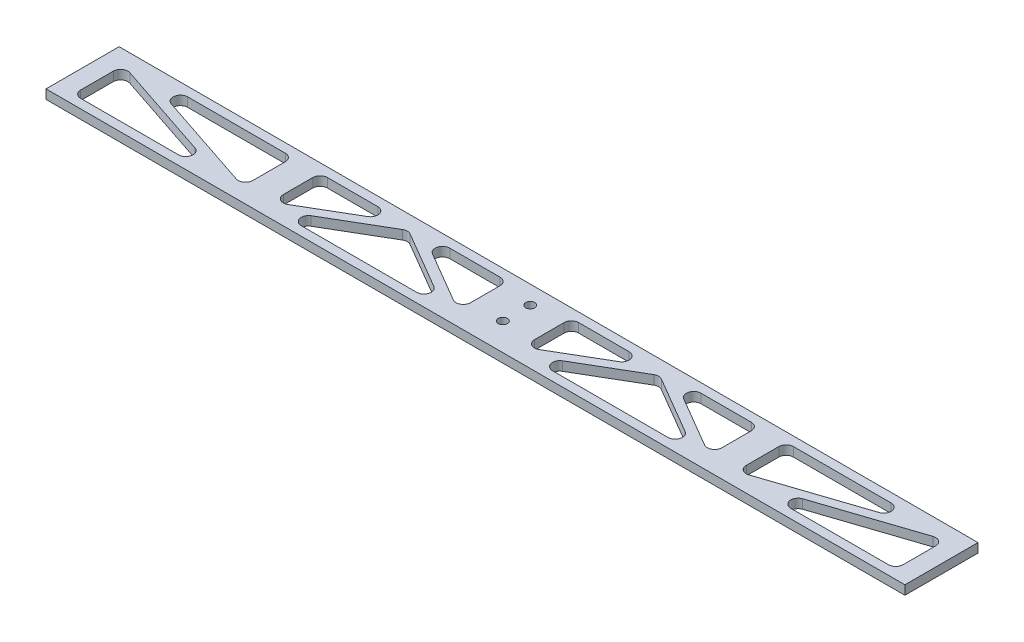
SolidWorks part; units mm, degrees
material "Balsa"
ref_plane "Front Plane" through (0, 0, 0) normal (0, 0, 1) x (1, 0, 0)
ref_plane "Top Plane" through (0, 0, 0) normal (0, 1, 0) x (1, 0, 0)
ref_plane "Right Plane" through (0, 0, 0) normal (1, 0, 0) x (0, 0, -1)
sketch "Sketch1" plane through (0, 0, 0) normal (0, 1, 0) x (1, 0, 0)
  line L1 (149.225, -12.7) -> (-149.225, -12.7)
  line L2 (149.225, -12.7) -> (149.225, 12.7)
  line L3 (149.225, 12.7) -> (-149.225, 12.7)
  line L4 (-149.225, -12.7) -> (-149.225, 12.7)
  point P0 (0, 12.7)
  point P6 (-149.225, 0)
  dimension "D1" = 25.4
  dimension "D2" = 298.45
extrude "Boss-Extrude1" add sketch "Sketch1" along normal blind 3.175
sketch "Sketch2" plane through (0, 3.175, 0) normal (0, 1, 0) x (1, 0, 0)
  line L0 (149.225, -12.7) -> (149.225, 12.7) construction
  line L2 (-149.225, 12.7) -> (-149.225, -12.7) construction
  line L4 (149.225, -12.7) -> (149.225, 12.7)
  line L6 (-149.225, 12.7) -> (-149.225, -12.7)
  line L8 (149.225, 9.525) -> (-149.225, 9.525)
  line L9 (-149.225, -9.525) -> (149.225, -9.525)
  line L10 (-142.875, 9.525) -> (-142.875, -9.525)
  line L11 (-80.9625, 9.525) -> (-80.9625, -9.525) construction
  line L12 (142.875, 9.525) -> (142.875, -9.525)
  line L13 (0, -9.525) -> (0, 9.525) construction
  line L14 (11.1125, 9.525) -> (11.1125, -9.525)
  line L15 (-11.1125, 9.525) -> (-11.1125, -9.525)
  line L16 (-85.725, 9.525) -> (-85.725, -9.525)
  line L17 (-76.2, 9.525) -> (-76.2, -9.525)
  line L18 (80.9625, 9.525) -> (80.9625, -9.525) construction
  line L19 (85.725, 9.525) -> (85.725, -9.525)
  line L20 (76.2, 9.525) -> (76.2, -9.525)
  line L21 (-76.2, -9.525) -> (-43.6562, 9.525)
  line L22 (-43.6562, 9.525) -> (-11.1125, -9.525)
  line L23 (-85.725, -9.525) -> (-142.875, 9.525)
  line L24 (11.1125, -9.525) -> (43.6562, 9.525)
  line L25 (43.6562, 9.525) -> (76.2, -9.525)
  line L26 (85.725, -9.525) -> (142.875, 9.525)
  line L27 (-85.223, -8.019) -> (-142.373, 11.031)
  line L28 (-75.398, -10.895) -> (-43.6562, 7.6855)
  line L29 (-43.6562, 7.6855) -> (-11.9145, -10.895)
  line L30 (11.9145, -10.895) -> (43.6562, 7.6855)
  line L31 (43.6562, 7.6855) -> (75.398, -10.895)
  line L32 (86.227, -11.031) -> (143.377, 8.019)
  line L33 (-86.227, -11.031) -> (-143.377, 8.019)
  line L34 (-77.002, -8.155) -> (-43.6562, 11.3645)
  line L35 (-43.6562, 11.3645) -> (-10.3105, -8.155)
  line L36 (10.3105, -8.155) -> (43.6562, 11.3645)
  line L37 (43.6562, 11.3645) -> (77.002, -8.155)
  line L38 (85.223, -8.019) -> (142.373, 11.031)
  dimension "D1" = 3.175
  dimension "D2" = 3.175
  dimension "D3" = 6.35
  dimension "D4" = 6.35
  dimension "D11" = 4.7625
  dimension "D12" = 4.7625
  dimension "D8" = 9.525
  dimension "D9" = 4.7625
  dimension "D7" = 63.5
  dimension "D10" = 63.5
  dimension "D5" = 22.225
  dimension "D6" = 11.1125
  dimension "D13" = 1.5875
  dimension "D14" = 1.5875
extrude "Cut-Extrude1" cut sketch "Sketch2" against normal through all contours L9 L33 L10 | L27 L16 L8 | L17 L34 L8 | L29 L28 L9 | L8 L35 L15 | L14 L36 L8 | L31 L30 L9 | L8 L37 L20 | L19 L38 L8 | L32 L9 L12
sketch "Sketch3" plane through (0, 3.175, 0) normal (0, 1, 0) x (1, 0, 0)
  circle A0 centre (0, 6.35) radius 1.5875
  circle A1 centre (0, -3.175) radius 1.5875
  dimension "D1" = 3.175
  dimension "D2" = 9.525
  dimension "D3" = 6.35
extrude "Cut-Extrude2" cut sketch "Sketch3" against normal through all
fillet "Fillet1" radius 2.54 30 edges at (-14.2549, 1.5875, 9.525) (-73.0576, 1.5875, 9.525) (-43.6562, 1.5875, -7.6855) (-11.1125, 1.5875, 7.6855) (-40.5138, 1.5875, -9.525) (-11.1125, 1.5875, -9.525) (-46.7987, 1.5875, -9.525) (-76.2, 1.5875, 7.6855) (-76.2, 1.5875, -9.525) (73.0576, 1.5875, 9.525) (14.2549, 1.5875, 9.525) (43.6562, 1.5875, -7.6855) (142.875, 1.5875, -7.8516) (142.875, 1.5875, 9.525) (90.7451, 1.5875, 9.525) (40.5138, 1.5875, -9.525) (11.1125, 1.5875, 7.6855) (11.1125, 1.5875, -9.525) (76.2, 1.5875, 7.6855) (46.7987, 1.5875, -9.525) (76.2, 1.5875, -9.525) (137.8549, 1.5875, -9.525) (85.725, 1.5875, 7.8516) (85.725, 1.5875, -9.525) (-137.8549, 1.5875, -9.525) (-85.725, 1.5875, 7.8516) (-85.725, 1.5875, -9.525) (-90.7451, 1.5875, 9.525) (-142.875, 1.5875, 9.525) (-142.875, 1.5875, -7.8516)
equation "\"D10@Sketch2\"=\"D7@Sketch2\""
equation "\"D6@Sketch2\"=\"D5@Sketch2\"/2"
